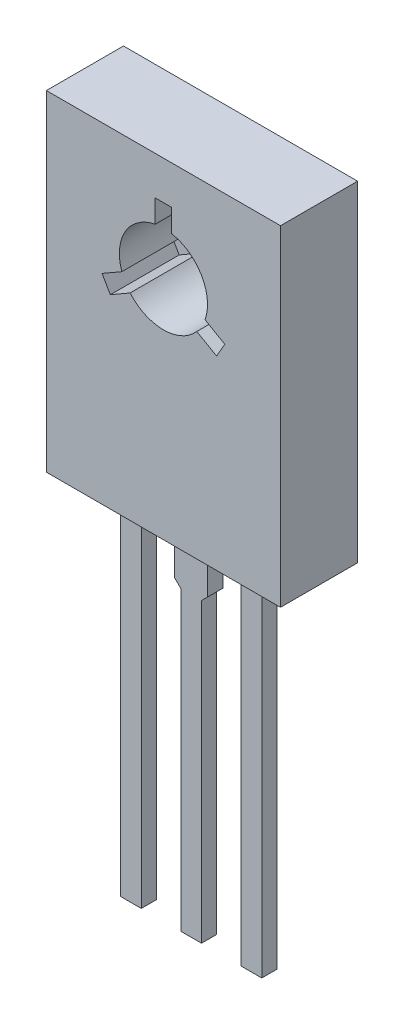
SolidWorks part; units mm, degrees
ref_plane "Front Plane" through (0, 0, 0) normal (0, 0, 1) x (1, 0, 0)
ref_plane "Top Plane" through (0, 0, 0) normal (0, 1, 0) x (1, 0, 0)
ref_plane "Right Plane" through (0, 0, 0) normal (1, 0, 0) x (0, 0, -1)
sketch "Sketch1" plane through (0, 0, 0) normal (0, 0, 1) x (1, 0, 0)
  line L1 (0, 0) -> (8.5, 0)
  line L2 (0, 0) -> (0, -12)
  line L3 (0, -12) -> (8.5, -12)
  line L4 (8.5, 0) -> (8.5, -12)
  circle A0 centre (4.25, -3.8) radius 1.6
  dimension "D3" = 3.2
  dimension "D1" = 8.5
  dimension "D2" = 12
  dimension "D4" = 3.8
extrude "Boss-Extrude1" add sketch "Sketch1" along normal blind 2.8
sketch "Sketch2" plane through (0, 0, 2.8) normal (0, 0, 1) x (1, 0, 0)
  line L0 (4.25, -2.2) -> (4.25, -1.4) construction
  line L1 (6.4785, -4.7402) -> (6.1785, -5.2598)
  line L2 (3.95, -1.4) -> (4.55, -1.4)
  line L3 (3.95, -1.4) -> (3.95, -2.2284)
  line L4 (3.95, -2.2284) -> (4.55, -2.2284)
  line L5 (4.55, -1.4) -> (4.55, -2.2284)
  line L6 (6.4785, -4.7402) -> (5.7611, -4.326)
  line L7 (5.7611, -4.326) -> (5.4611, -4.8456)
  line L8 (6.1785, -5.2598) -> (5.4611, -4.8456)
  line L10 (5.6356, -4.6) -> (6.3285, -5) construction
  line L11 (2.3215, -5.2598) -> (2.0215, -4.7402)
  line L12 (2.3215, -5.2598) -> (3.0389, -4.8456)
  line L13 (3.0389, -4.8456) -> (2.7389, -4.326)
  line L15 (2.0215, -4.7402) -> (2.7389, -4.326)
  line L16 (2.8644, -4.6) -> (2.1715, -5) construction
  circle A0 centre (4.25, -3.8) radius 1.6 construction
  arc A1 (3.95, -2.2284) -> (4.55, -2.2284) centre (4.25, -3.8) cw
  arc A5 (5.7611, -4.326) -> (5.4611, -4.8456) centre (4.25, -3.8) cw
  arc A6 (3.0389, -4.8456) -> (2.7389, -4.326) centre (4.25, -3.8) cw
  point P7 (4.25, -3.8)
  point P26 (4.25, -3.8)
  circle M12 centre (4.25, -3.8) radius 1.6
  dimension "D1" = 0.8
  dimension "D2" = 0.6
  dimension "D3" = 3
extrude "Cut-Extrude1" cut sketch "Sketch2" against normal blind 2.5 contours L15 L11 L12 M12 | L8 L1 L6 M12 | L5 L2 L3 M12
sketch "Sketch3" plane through (0, -12, 0) normal (0, -1, 0) x (1, 0, 0)
  line L0 (2.2142, 1.5198) -> (6.8142, 1.5198) construction
  line L1 (1.69, 1.7948) -> (2.44, 1.7948)
  line L2 (1.69, 1.7948) -> (1.69, 1.2448)
  line L3 (1.69, 1.2448) -> (2.44, 1.2448)
  line L4 (2.44, 1.7948) -> (2.44, 1.2448)
  line L5 (3.8771, 1.7948) -> (4.6271, 1.7948)
  line L6 (3.8771, 1.7948) -> (3.8771, 1.2448)
  line L7 (3.8771, 1.2448) -> (4.6271, 1.2448)
  line L8 (4.6271, 1.7948) -> (4.6271, 1.2448)
  line L9 (6.0642, 1.7948) -> (6.8142, 1.7948)
  line L10 (6.0642, 1.7948) -> (6.0642, 1.2448)
  line L11 (6.0642, 1.2448) -> (6.8142, 1.2448)
  line L12 (6.8142, 1.7948) -> (6.8142, 1.2448)
  line L13 (0, 2.8) -> (0, 0) construction
  point P4 (2.2142, 1.5198)
  point P12 (4.4014, 1.5198)
  point P17 (6.5885, 1.5198)
  dimension "D1" = 0.75
  dimension "D2" = 0.55
  dimension "D3" = 4.6
  dimension "D5" = 0
  dimension "D6" = 5.1242
  dimension "D7" = 1.69
  dimension "D4" = 3
extrude "Boss-Extrude2" add sketch "Sketch3" along normal blind 13
sketch "Sketch4" plane through (0, 0, 1.7948) normal (0, 0, 1) x (1, 0, 0)
  line L0 (3.6521, -14) -> (4.1521, -14.5)
  line L5 (4.2521, -12) -> (4.2521, -14.5) construction
  line L6 (4.6271, -12) -> (3.8771, -12) construction
  line L7 (0, -12) -> (8.5, -12) construction
  line L8 (3.6521, -12) -> (4.8521, -12)
  line L9 (3.6521, -12) -> (3.6521, -14)
  line L10 (4.1521, -14.5) -> (4.3521, -14.5)
  line L11 (4.8521, -12) -> (4.8521, -14)
  line L12 (4.3521, -14.5) -> (4.8521, -14)
  point P6 (4.8521, -14.5)
  point P7 (3.6521, -14.5)
  dimension "D1" = 2.5
  dimension "D2" = 1.2
  dimension "D3" = 0.6
extrude "Boss-Extrude3" add sketch "Sketch4" against normal blind 0.55
sketch "Sketch5" plane through (0, 0, 0) normal (0, 0, -1) x (-1, 0, 0)
  line L0 (-8.5, 0) -> (0, 0) construction
  line L1 (-7.25, -1) -> (-1.25, -1)
  line L2 (-7.25, -1) -> (-7.25, -9)
  line L3 (-7.25, -9) -> (-1.25, -9)
  line L4 (-1.25, -1) -> (-1.25, -9)
  line L5 (-8.5, -12) -> (-8.5, 0) construction
  circle A0 centre (-4.25, -3.8) radius 1.6
  dimension "D1" = 8
  dimension "5" = 6
  dimension "D2" = 1
  dimension "D3" = 1.25
extrude "Boss-Extrude4" add sketch "Sketch5" along normal blind 0.001
